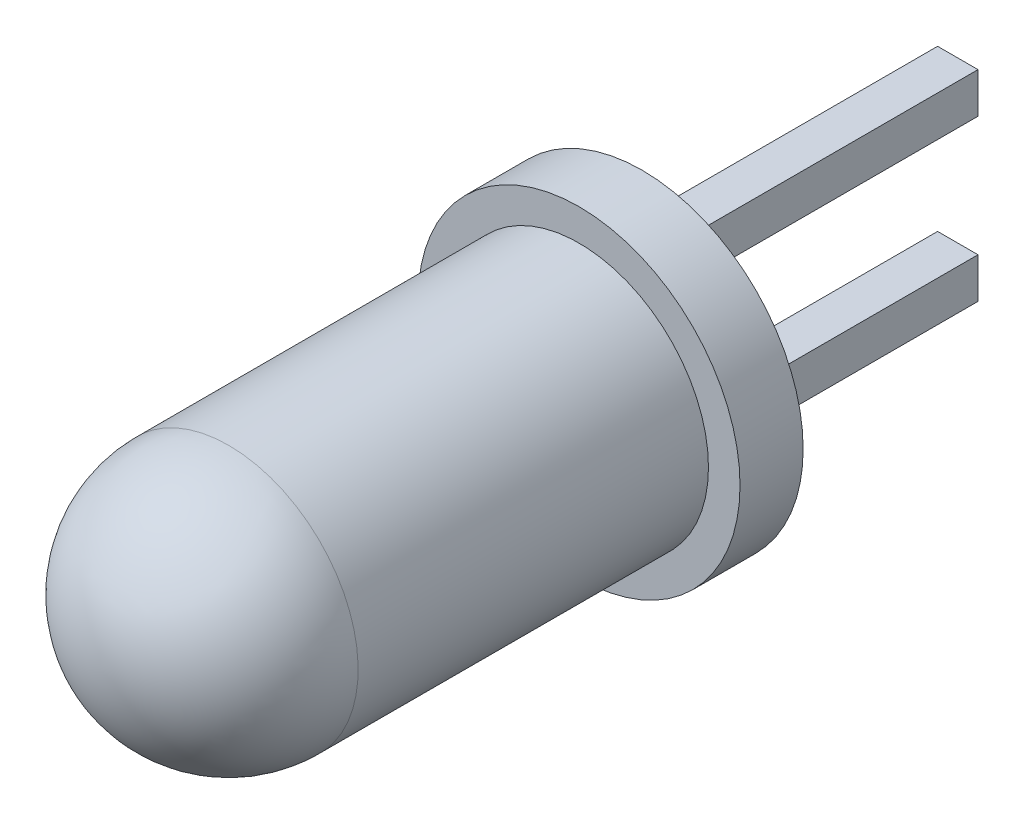
SolidWorks part; units mm, degrees
ref_plane "Front Plane" through (0, 0, 0) normal (0, 0, 1) x (1, 0, 0)
ref_plane "Top Plane" through (0, 0, 0) normal (0, 1, 0) x (1, 0, 0)
ref_plane "Right Plane" through (0, 0, 0) normal (1, 0, 0) x (0, 0, -1)
sketch "Sketch2" plane through (0, 0, 0) normal (1, 0, 0) x (0, 0, -1)
  line L0 (0, 0) -> (0, 2.55)
  line L1 (0, 2.55) -> (-1, 2.55)
  line L2 (-1, 2.55) -> (-1, 2.05)
  line L3 (-1, 2.05) -> (-6.55, 2.05)
  line L4 (0, 2.55) -> (0, -2.55) construction
  line L5 (-8.6, 0) -> (0, 0)
  line L6 (0, 0) -> (-8.6, 0) construction
  arc A0 (-6.55, 2.05) -> (-8.6, 0) centre (-6.55, 0) ccw
  dimension "D1" = 1
  dimension "D2" = 5.1
  dimension "D3" = 0.5
  dimension "D4" = 8.6
revolve "Base-Revolve" add sketch "Sketch2" angle 360 about L6
sketch "Sketch3" plane through (0, 0, 0) normal (0, 0, -1) x (-1, 0, 0)
  line L0 (0, 1.27) -> (0, -1.27) construction
  line L1 (-0.32, 1.59) -> (0.32, 1.59)
  line L2 (-0.32, 1.59) -> (-0.32, 0.95)
  line L3 (0.32, 0.95) -> (-0.32, 0.95)
  line L4 (0.32, 0.95) -> (0.32, 1.59)
  line L5 (-0.32, -0.95) -> (0.32, -0.95)
  line L6 (-0.32, -0.95) -> (-0.32, -1.59)
  line L7 (0.32, -1.59) -> (-0.32, -1.59)
  line L8 (0.32, -1.59) -> (0.32, -0.95)
  line L9 (-0.32, 1.59) -> (0.32, 0.95) construction
  line L10 (-0.32, -0.95) -> (0.32, -1.59) construction
  point P4 (0, 0)
  point P12 (0, -1.27)
  point P13 (0, 1.27)
  dimension "D2" = 0.64
  dimension "D1" = 2.54
extrude "Boss-Extrude1" add sketch "Sketch3" along normal blind 5
ref_plane "Mounting Plane" through (0, 0, -1.5) normal (0, 0, 1) x (1, 0, 0)
sketch "Component_Outline" plane through (0, 0, -1.5) normal (0, 0, 1) x (1, 0, 0)
  circle A0 centre (0, 0) radius 2.55
  dimension "D1" = 5.1
